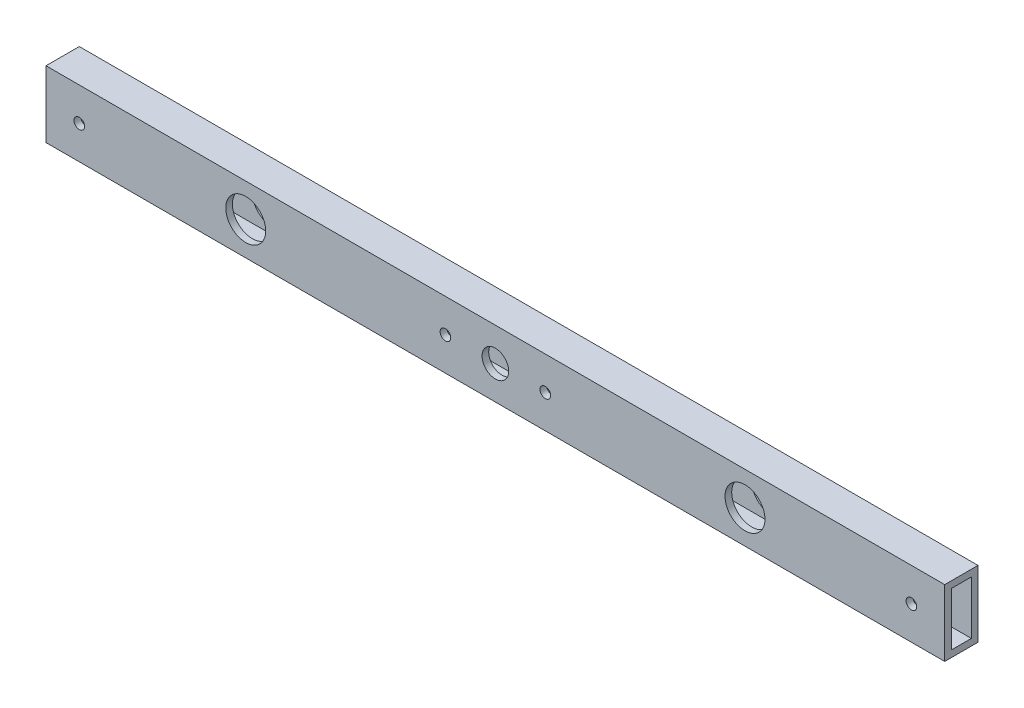
SolidWorks part; units mm, degrees
material "6061 合金"
ref_plane "前视基准面" through (0, 0, 0) normal (0, 0, 1) x (1, 0, 0)
ref_plane "上视基准面" through (0, 0, 0) normal (0, 1, 0) x (1, 0, 0)
ref_plane "右视基准面" through (0, 0, 0) normal (1, 0, 0) x (0, 0, -1)
sketch "草图1" plane through (0, 0, 0) normal (0, 1, 0) x (1, 0, 0)
  line L0 (0, 0) -> (270, 0)
  dimension "D1" = 270
other "铝方管 20X10X2(2)"
ref_plane "基准面1" through (0, 0, 0) normal (1, 0, 0) x (0, 0, -1)
sketch "草图15" plane through (0, 0, 0) normal (1, 0, 0) x (0, 0, -1)
  line L0 (-3, 8) -> (3, 8)
  line L1 (-5, -10) -> (5, -10)
  line L2 (-5, -10) -> (-5, 10)
  line L3 (-5, 10) -> (5, 10)
  line L4 (5, -10) -> (5, 10)
  line L5 (-5, -10) -> (5, 10) construction
  line L6 (-5, 10) -> (5, -10) construction
  line L7 (3, -8) -> (3, 8)
  line L8 (-3, -8) -> (3, -8)
  line L9 (-3, -8) -> (-3, 8)
  point P0 (0, 0)
  point P10 (-5, 0)
  point P11 (5, 0)
  point P12 (0, 10)
  point P13 (0, -10)
  point P14 (0, 0)
  dimension "D1" = 10
  dimension "D2" = 20
  dimension "D3" = 2
sketch "草图12" plane through (0, 0, 5) normal (0, 0, 1) x (1, 0, 0)
  line L0 (270, 0) -> (0, 0) construction
  line L1 (270, 10) -> (270, -10) construction
  line L2 (135, -10) -> (135, 10) construction
  line L6 (270, 10) -> (0, 10) construction
  line L7 (270, -10) -> (0, -10) construction
  circle A0 centre (10, 0) radius 1.6
  circle A1 centre (260, 0) radius 1.6
  dimension "D1" = 3.2
  dimension "D2" = 250
extrude "切除-拉伸1" cut sketch "草图12" against normal through all
sketch "草图16" plane through (0, 0, 5) normal (0, 0, 1) x (1, 0, 0)
  line L0 (0, 0) -> (270, 0) construction
  line L1 (0, -10) -> (0, 10) construction
  line L2 (270, 10) -> (270, -10) construction
  line L3 (135, 10) -> (135, -10) construction
  line L4 (270, 10) -> (0, 10) construction
  line L5 (270, -10) -> (0, -10) construction
  circle A0 centre (60, 0) radius 6
  circle A1 centre (210, 0) radius 6
  dimension "D1" = 12
  dimension "D2" = 150
extrude "切除-拉伸2" cut sketch "草图16" against normal through all
sketch "草图17" plane through (0, 0, 5) normal (0, 0, 1) x (1, 0, 0)
  line L0 (135, 10) -> (135, -10) construction
  line L1 (270, 10) -> (0, 10) construction
  line L2 (270, -10) -> (0, -10) construction
  circle A0 centre (135, 0) radius 4
  dimension "D1" = 8
extrude "切除-拉伸3" cut sketch "草图17" against normal blind 18
sketch "草图18" plane through (0, 0, 5) normal (0, 0, 1) x (1, 0, 0)
  line L0 (150, 0) -> (120, 0) construction
  circle A0 centre (120, 0) radius 1.6
  circle A1 centre (150, 0) radius 1.6
  point P5 (135, 0)
  dimension "D1" = 30
  dimension "D2" = 3.2
extrude "切除-拉伸4" cut sketch "草图18" against normal blind 10
